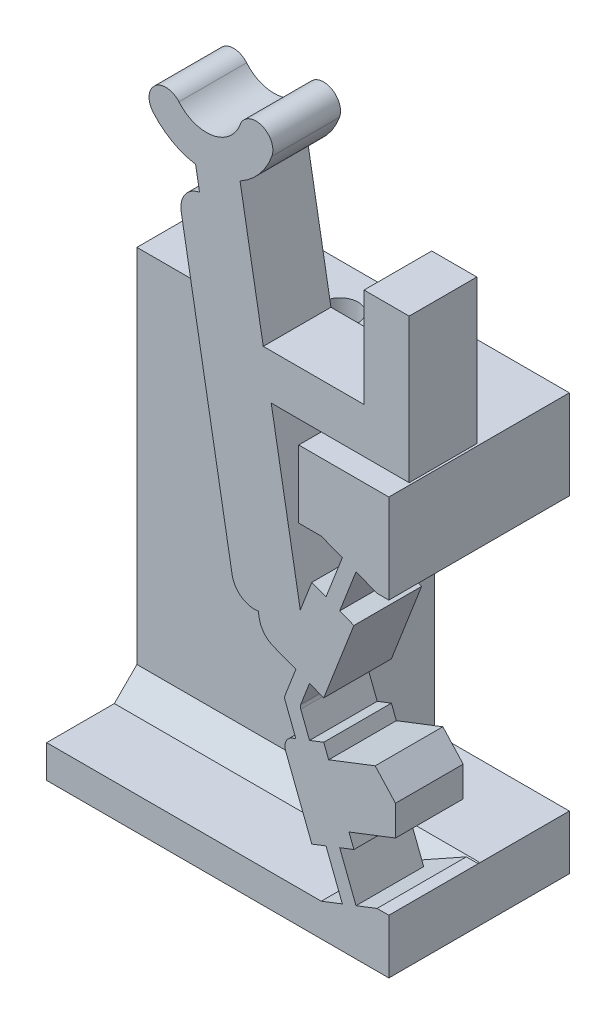
SolidWorks part; units mm, degrees
material "Nylon 6/12"
ref_plane "Front Plane" through (0, 0, 0) normal (0, 0, 1) x (1, 0, 0)
ref_plane "Top Plane" through (0, 0, 0) normal (0, 1, 0) x (1, 0, 0)
ref_plane "Right Plane" through (0, 0, 0) normal (1, 0, 0) x (0, 0, -1)
sketch "Sketch-SkeletonConfigUp" plane through (0, 0, 0) normal (0, 0, 1) x (1, 0, 0)
  line L0 (0, 0) -> (0, -50000) construction
  line L1 (-1.4217, 8.457) -> (-1.4217, 0) construction
  line L3 (0.7468, 14.0514) -> (-1.4217, 8.457) construction
  line L4 (-1.4217, 8.457) -> (0.7468, 2.8626) construction
  line L5 (0.7468, 14.0514) -> (2.1074, 19.3343) construction
  line L6 (-1.4217, 8.457) -> (-5.2203, 30) construction
  line L9 (0.7468, 14.0514) -> (0.7468, 2.8626) construction
  line L10 (0.7468, 2.8626) -> (0.7468, 0) construction
  line L11 (0, 0) -> (0.7468, 0) construction
  line L12 (0.7468, 0) -> (0, 0) construction
  dimension "D7" = 5.4552
  dimension "D10" = 6.745
  dimension "D3" = 2.1685
  dimension "D9" = 10
  dimension "D13" = 11.1888
  dimension "D14" = 30
  dimension "D5" = 10
  dimension "D2" = 21.8753
  dimension "D4" = 6
sketch "Sketch-SkeletonConfigDown" plane through (0, 0, 0) normal (0, 0, 1) x (1, 0, 0)
  line L0 (0, 0) -> (0, -50000) construction
  line L1 (0.7468, 14.0514) -> (0.7468, 2.8626) construction
  line L2 (5.9945, 14.5439) -> (0.7468, 14.0514) construction
  line L3 (0.7468, 14.0514) -> (2.9153, 8.457) construction
  line L4 (2.9153, 8.457) -> (0.7468, 2.8626) construction
  line L5 (0.7468, 14.0514) -> (-1.8086, 18.8711) construction
  line L6 (2.9153, 8.457) -> (-14.411, 21.8109) construction
  line L7 (0.7468, 2.8626) -> (5.9945, 14.5439) construction
  line L8 (-387.6937, -861.8102) -> (5.9945, 14.5439) construction
  line L10 (-1.4217, 8.457) -> (0.7468, 2.8626) construction
  line L11 (0.7468, 14.0514) -> (-1.4217, 8.457) construction
  line L12 (-1.4217, 8.457) -> (-5.2203, 30) construction
  line L13 (0.7468, 14.0514) -> (2.1074, 19.3343) construction
  dimension "D10" = 6.745
  dimension "D4" = 5.2707
  dimension "D5" = 119.553
  dimension "D2" = 52.378
  dimension "D3" = 31.19
ref_plane "Plane-Cam Base" through (3.8672, 0, 0) normal (1, 0, 0) x (0, 0, -1)
ref_plane "Plane-Down-to-Up Derailleur Clearance" through (1.3672, 0, 0) normal (1, 0, 0) x (0, 0, -1)
ref_plane "Plane-Cam Cavity Roof" through (-0.1328, 0, 0) normal (1, 0, 0) x (0, 0, -1)
sketch "Sketch-SwitchBossUp" plane through (0, 0, 0) normal (0, 0, 1) x (1, 0, 0)
  line L8 (-5.6979, 26.9497) -> (-5.5242, 25.9649)
  line L9 (-1.4217, 8.457) -> (-5.2203, 30) construction
  line L15 (-1.2549, 7.1274) -> (-0.6488, 7.3624) construction
  line L16 (-1.4217, 8.457) -> (0.7468, 2.8626) construction
  line L19 (0.0824, 13.2365) -> (0.6884, 13.0016) construction
  line L22 (0.8052, 15.1013) -> (1.4113, 14.8664) construction
  line L23 (-1.2549, 9.7866) -> (-1.8843, 10.0306)
  line L32 (1.0498, 2.9801) -> (0.4438, 2.7452) construction
  line L40 (-1.7703, 8.457) -> (-1.0732, 8.457) construction
  line L66 (-5.2203, 27.8193) -> (-5.2203, 50027.8193) construction
  line L74 (-4.078, 12.0039) -> (-6.3354, 24.8064)
  line L81 (2.3437, 2.4091) -> (2.8672, 2.4091)
  line L82 (-5.6111, 26.4573) -> (-3.6415, 26.8046) construction
  line L88 (-0.1116, 18.4627) -> (2.8672, 18.4627)
  line L92 (0.6492, 5.8814) -> (-1.2156, 5.1585) construction
  line L95 (-2.3469, 19.4627) -> (3.7672, 19.4627)
  line L96 (2.8672, 14.505) -> (2.8672, 18.4627)
  line L97 (3.7672, 19.4627) -> (3.7672, 25.8576)
  line L101 (-0.9519, 7.2449) -> (-1.4217, 8.457) construction
  line L103 (-5.2203, 30) -> (-3.0238, 29.2005) construction
  line L107 (-1.2549, 9.7866) -> (-0.6488, 9.5517) construction
  line L109 (-5.2203, 30) -> (-7.011, 28.4975) construction
  line L114 (-0.0195, 7.6063) -> (-0.6488, 7.3624)
  line L117 (2.8672, 0) -> (-0.1272, 0)
  line L121 (0.7468, 0) -> (0, 0) construction
  line L122 (0.8052, 1.8128) -> (-0.1272, 1.4513)
  line L123 (1.4113, 2.0477) -> (2.3437, 2.4091)
  line L125 (2.8672, 2.4091) -> (2.8672, 0)
  line L127 (-0.6488, 9.5517) -> (-0.0195, 9.3077)
  line L133 (0.4438, 14.1689) -> (1.0498, 13.934) construction
  line L134 (-0.0195, 9.3077) -> (1.3178, 12.7576)
  line L135 (0.6884, 13.0016) -> (1.3178, 12.7576)
  line L142 (-0.1272, 1.4513) -> (-0.1272, 0)
  line L151 (0.0824, 13.2365) -> (-0.547, 13.4805)
  line L152 (0.8052, 15.1013) -> (0.0824, 13.2365)
  line L153 (1.4113, 14.8664) -> (0.6884, 13.0016)
  line L169 (0.0824, 3.6776) -> (0.8052, 1.8128)
  line L170 (1.4113, 2.0477) -> (0.6884, 3.9125)
  line L177 (0.6884, 3.9125) -> (0.0824, 3.6776) construction
  line L184 (-0.547, 13.4805) -> (-1.0591, 12.1594)
  line L191 (-1.2549, 7.1274) -> (-1.8843, 6.8835)
  line L197 (3.7672, 25.8576) -> (1.7672, 25.8576)
  line L205 (1.7672, 25.8576) -> (1.7672, 21.4627)
  line L207 (12.0045, 16.6962) -> (12.0045, 16.6883) construction
  line L218 (0.6884, 3.9125) -> (1.3178, 4.1564)
  line L225 (-1.0591, 12.1594) -> (-2.3469, 19.4627)
  line L235 (-5.5242, 25.9649) -> (-2.7755, 10.376) construction
  line L236 (-1.8843, 6.8835) -> (-0.547, 3.4336)
  line L237 (-2.7755, 10.376) -> (-2.9195, 11.1927)
  line L241 (-1.4217, 8.457) -> (-0.9519, 9.6692) construction
  line L242 (1.7672, 21.4627) -> (-2.6996, 21.4627)
  line L243 (-0.6488, 7.3624) -> (-1.0381, 8.3667)
  line L244 (-1.0381, 8.5474) -> (-0.6488, 9.5517)
  line L245 (-1.2549, 7.1274) -> (-1.7353, 8.3667)
  line L246 (-1.7353, 8.5474) -> (-1.2549, 9.7866)
  line L247 (-0.0195, 7.6063) -> (0.1991, 7.0424)
  line L248 (0.8052, 1.8128) -> (1.4113, 2.0477) construction
  line L249 (0.0824, 3.6776) -> (-0.547, 3.4336)
  line L250 (-1.8843, 10.0306) -> (-0.547, 13.4805) construction
  line L251 (0.7468, 14.0514) -> (-1.4217, 8.457) construction
  line L252 (-1.2699, 11.6157) -> (0.5949, 10.8928) construction
  line L253 (-2.3469, 19.4627) -> (-2.6996, 21.4627) construction
  line L254 (-1.8843, 10.0306) -> (-2.7755, 10.376)
  line L255 (0.8052, 15.1013) -> (-0.1272, 15.4627)
  line L256 (1.4113, 14.8664) -> (2.3437, 14.505)
  line L257 (2.3437, 14.505) -> (2.8672, 14.505)
  line L258 (-2.6996, 21.4627) -> (-3.7283, 27.297)
  line L259 (3.8672, -55) -> (3.8672, 55) construction
  line L260 (0.1991, 7.0424) -> (2.2611, 7.8417)
  line L261 (3.1613, 6.8552) -> (3.1613, 5.5197)
  line L262 (3.1613, 5.5197) -> (1.0992, 4.7204)
  line L263 (0.6492, 5.8814) -> (3.1613, 6.8552) construction
  line L264 (1.0992, 4.7204) -> (0.6492, 5.8814) construction
  line L265 (1.0992, 4.7204) -> (1.3178, 4.1564)
  line L266 (0.6492, 5.8814) -> (0.1991, 7.0424) construction
  line L267 (0.1991, 7.0424) -> (0.6492, 5.8814) construction
  line L268 (0.6492, 5.8814) -> (1.0992, 4.7204) construction
  line L269 (0.1991, 7.0424) -> (0.6492, 5.8814) construction
  line L270 (0.6492, 5.8814) -> (1.0992, 4.7204) construction
  line L271 (3.1613, 6.8552) -> (2.2611, 7.8417)
  line L272 (1.8311, 5.6598) -> (3.8672, 4.8706) construction
  line L273 (2.9153, 8.457) -> (0.7468, 2.8626) construction
  line L274 (-0.2832, 5.52) -> (2.2611, 7.8417) construction
  line L275 (-0.2832, 5.52) -> (3.8672, 5.52) construction
  line L276 (-0.1272, 15.4627) -> (-1.1272, 15.4627)
  line L277 (-1.1272, 15.4627) -> (-1.1272, 18.4627)
  line L278 (-1.1272, 18.4627) -> (-0.1116, 18.4627)
  arc A0 (-3.7283, 27.297) -> (-2.319, 28.944) centre (-5.2203, 30) ccw
  arc A1 (-5.6979, 26.9497) -> (-7.5855, 28.0154) centre (-5.2203, 30) cw
  arc A2 (-7.5855, 28.0154) -> (-6.4364, 28.9796) centre (-7.011, 28.4975) cw
  arc A3 (-2.319, 28.944) -> (-3.7286, 29.457) centre (-3.0238, 29.2005) ccw
  arc A4 (-6.4364, 28.9796) -> (-3.7286, 29.457) centre (-5.2203, 30) ccw
  arc A19 (-6.3354, 24.8064) -> (-5.5242, 25.9649) centre (-5.3506, 24.98) cw
  circle A28 centre (-5.2203, 30) radius 2.3375 construction
  arc A30 (-4.078, 12.0039) -> (-2.9195, 11.1927) centre (-3.0932, 12.1775) ccw
  arc A31 (-1.0381, 8.3667) -> (-1.0381, 8.5474) centre (-0.805, 8.457) cw
  arc A32 (-1.7353, 8.3667) -> (-1.7353, 8.5474) centre (-1.5022, 8.457) cw
  point P5 (-4.6263, 26.6309)
  point P6 (-0.2832, 5.52)
  point P45 (-0.3375, 11.2542)
  point P66 (4.5811, 6.2164)
  point P165 (0.7468, 14.0514)
  dimension "D23" = 1.5875
  dimension "D24" = 0.75
  dimension "D21" = 0.25
  dimension "D8" = 0.65
  dimension "D27" = 0.65
  dimension "D26" = 2
  dimension "D3" = 1.3
  dimension "D5" = 1.3
  dimension "D16" = 2
  dimension "D28" = 2
  dimension "D29" = 2
  dimension "D30" = 1
  dimension "D31" = 15
  dimension "D4" = 1.4169
  dimension "D6" = 0.65
  dimension "D7" = 2
  dimension "D11" = 1
  dimension "D10" = 1
  dimension "D9" = 0
  dimension "D12" = 60
  dimension "D13" = 60
  dimension "D14" = 2
  dimension "D15" = 1
  dimension "D17" = 2
  dimension "D19" = 0.1
  dimension "D22" = 42.38
  dimension "D18" = 3
  dimension "D25" = 1
  dimension "D32" = 1
  dimension "D20" = 1
extrude "Boss-Switch Body" add sketch "Sketch-SwitchBossUp" along normal blind 3
sketch "Sketch1" plane through (0, 0, 0) normal (0, 0, -1) x (-1, 0, 0)
  line L0 (-2.8672, 2.4091) -> (0.1272, 2.4091)
  line L1 (-2.8672, 0) -> (0.1272, 0)
  line L2 (-2.8672, 0) -> (-2.8672, 2.4091)
  line L4 (0.1272, 0) -> (0.1272, 2.4091)
  line L5 (1.1272, 14.505) -> (-2.8672, 14.505)
  line L10 (-2.8672, 14.505) -> (-2.8672, 18.4627)
  line L12 (-2.8672, 18.4627) -> (1.1272, 18.4627)
  line L14 (1.1272, 18.4627) -> (1.1272, 14.505)
  line L20 (-2.3437, 2.4091) -> (-2.8672, 2.4091) construction
  line L22 (-2.8672, 2.4091) -> (-2.3437, 2.4091) construction
  line L31 (0.1272, 0) -> (-2.8672, 0) construction
  line L32 (0.1272, 1.4513) -> (0.1272, 0) construction
extrude "Boss-Flange Width" add sketch "Sketch1" along normal blind 5
ref_plane "Plane-Sta2Sit Groove" through (-5.2203, 0, 0) normal (1, 0, 0) x (0, 0, -1)
ref_plane "Plane-Cam Outer Surface" through (-17.3003, 0, 0) normal (1, 0, 0) x (0, 0, -1)
ref_plane "Plane-FlangeTop" through (-12.3003, 0, 0) normal (1, 0, 0) x (0, 0, -1)
sketch "Sketch2" plane through (-12.3003, 0, 0) normal (1, 0, 0) x (0, 0, -1)
  line L0 (5, 18.4627) -> (-3, 18.4627) construction
  line L1 (5, 14.505) -> (1, 14.505)
  line L2 (5, 14.505) -> (5, 18.4627)
  line L3 (5, 18.4627) -> (1, 18.4627)
  line L4 (1, 14.505) -> (1, 18.4627)
  line L5 (5, 14.505) -> (-3, 14.505) construction
  line L11 (5, 1.4513) -> (-3, 1.4513)
  line L12 (5, 1.4513) -> (5, 0)
  line L13 (5, 0) -> (-3, 0)
  line L14 (-3, 1.4513) -> (-3, 0)
  line L15 (0, 8.457) -> (0, 30) construction
  line L16 (-3, 1.4513) -> (-3, 0) construction
  line L17 (5, 2.4091) -> (5, 0) construction
  line L19 (-3, 1.4513) -> (0, 1.4513) construction
  dimension "D1" = 1
extrude "Boss-Flange Height" add sketch "Sketch2" along normal up to surface (12.1731 mm away) up to face at (-0.1272, 1.2868, -0.6667)
sketch "Sketch17" plane through (0, 1.4513, 0) normal (0, -1, 0) x (1, 0, 0)
  line L0 (2.8672, -5) -> (-12.3003, -5)
  line L1 (2.8672, -5) -> (-12.3003, -5) construction
  line L2 (-12.3003, -5) -> (-12.3003, -1)
  line L3 (-12.3003, -1) -> (2.8672, -1)
  line L4 (2.8672, -1) -> (2.8672, -5)
  line L5 (-12.3003, -1) -> (-12.3003, -5) construction
  line L7 (-1.1272, -1) -> (-12.3003, -1) construction
extrude "Boss-Flange Support" add sketch "Sketch17" against normal up to surface (13.0536 mm away) up to face at (-1.4588, 14.505, -0.6)
sketch "Sketch27" plane through (0, 0, 0) normal (0, 0, 1) x (1, 0, 0)
  line L1 (-0.1272, 15.4627) -> (2.3437, 14.505)
  line L2 (2.3437, 14.505) -> (-1.1272, 14.505)
  line L3 (-1.1272, 14.505) -> (-1.1272, 15.4627)
  line L4 (-1.1272, 15.4627) -> (-0.1272, 15.4627)
  line L6 (-1.1272, 14.505) -> (2.8672, 14.505) construction
  line L7 (2.3437, 14.505) -> (1.2712, 14.505) construction
  line L8 (2.3437, 2.4091) -> (-0.1272, 2.4091)
  line L9 (-0.1272, 2.4091) -> (-0.1272, 1.4513)
  line L10 (-0.1272, 1.4513) -> (2.3437, 2.4091)
extrude "Cut-Wall Gap" cut sketch "Sketch27" against normal up to surface (1 mm away) up to face at (-2.6719, 9.207, -1)
ref_plane "Plane-Tap Depth" through (0, 13.4627, 0) normal (0, 1, 0) x (1, 0, 0)
sketch "Sketch-HolePositions" plane through (0, 0, 0) normal (0, -1, 0) x (1, 0, 0)
  line L0 (-12.3003, -3) -> (2.8672, -3) construction
  line L1 (2.8672, -5) -> (-12.3003, -5) construction
  line L2 (2.8672, -5) -> (2.8672, 3) construction
  line L4 (-12.3003, -22.2167) -> (-12.3003, 22.2167) construction
  point P6 (-9.3003, -3)
  point P7 (-5.3003, -3)
  dimension "D1" = 3
  dimension "D2" = 4
  dimension "D3" = 2
sketch "Sketch6" plane through (0, 0, 0) normal (0, -1, 0) x (-1, 0, 0)
  point P0 (9.3003, 3)
  point P3 (5.3003, 3)
hole_wizard "Tap Drill for M2x0.4 Tap1" positions "Sketch6" profile "Sketch5" hole size "M2x0.4" standard "ANSI Metric" end condition through all
sketch "Sketch5" plane through (-9.3003, 0, -3) normal (1, 0, 0) x (0, 0, -1)
  line L0 (0, 0) -> (0, 29.9505)
  line L1 (0, 29.9505) -> (0.8, 29.9505)
  line L2 (0.8, 29.9505) -> (0.8, 0)
  line L5 (0.8, 0) -> (0, 0)
  line L11 (0, -6.35) -> (0, 107.95) construction
  dimension "Thru Hole Dia." = 1.6
  dimension "Thru Hole Depth" = 29.9505
sketch "Sketch9" plane through (0, 0, 0) normal (0, -1, 0) x (1, 0, 0)
  point P0 (-9.3003, -3)
  point P3 (-5.3003, -3)
hole_wizard "M2 Clearance Hole2" positions "Sketch9" profile "Sketch8" hole size "M2" standard "ANSI Metric"
sketch "Sketch8" plane through (-9.3003, 0, -3) normal (1, 0, 0) x (0, 0, -1)
  line L0 (0, 0) -> (0, 14.1838)
  line L1 (0, 14.1838) -> (1.2, 13.4627)
  line L2 (1.2, 13.4627) -> (1.2, 0)
  line L5 (1.2, 0) -> (0, 0)
  line L10 (0, 14.1838) -> (-1.2, 13.4627) construction
  line L11 (0, -6.35) -> (0, 107.95) construction
  dimension "Hole Dia." = 2.4
  dimension "Hole Depth" = 13.4627
  dimension "Drill Angle" = 118
sketch "Sketch-Measurements for Derailleur Ramps" [suppressed] plane through (0, 0, 0) normal (0, 0, 1) x (1, 0, 0)
  line L0 (2.8784, 16.9852) -> (4.2265, 19.8331)
  line L1 (3.5524, 18.4092) -> (3.0492, 18.6474)
  line L2 (1.9779, 11.0613) -> (4.4465, 28.5428) construction
  line L3 (3.0492, 18.6474) -> (-4.0642, 13.8428)
  line L4 (7.1843, 11.0614) -> (-9.9544, 15.2993) construction
  line L5 (3.0492, 18.6474) -> (2.1536, 12.3053)
  line L6 (2.1536, 12.3053) -> (-4.0642, 13.8428)
  line L7 (-0.5075, 16.2451) -> (-0.5075, 18.6474)
  line L8 (-0.5075, 18.6474) -> (3.0492, 18.6474)
  line L9 (7.1843, 11.0614) -> (1.9779, 11.0613)
  line L10 (5.8827, 8.6389) -> (3.2795, 8.6389)
  line L12 (7.1843, 11.0614) -> (4.5811, 6.2164) construction
  line L13 (4.5811, 8.6389) -> (4.5811, 8.7912)
  line L14 (4.5811, 6.2164) -> (5.8827, 8.6389)
  line L15 (1.9779, 11.0613) -> (4.5811, 6.2164) construction
  line L16 (3.2795, 8.6389) -> (4.5811, 6.2164)
  line L17 (5.8827, 8.6389) -> (5.8827, 8.7912)
  dimension "D1" = 3.5567
  dimension "D2" = 1.3016
sketch "Sketch12" [suppressed] plane through (0, 23.1883, 0) normal (0, 1, 0) x (1, 0, 0)
  line L0 (10.0045, 0) -> (12.0045, -3)
  line L1 (12.0045, -3) -> (12.0045, 0)
  line L2 (12.0045, 0) -> (10.0045, 0)
extrude "Cut-Up-to-Down Cantilever Slope" [suppressed] cut sketch "Sketch12" against normal up to next
ref_plane "Plane1" [suppressed] through (0, 6.9404, 0) normal (0, 1, 0) x (1, 0, 0)
sketch "Sketch-Derailleur Location" [suppressed] plane through (0, 6.9404, 0) normal (0, 1, 0) x (1, 0, 0)
  line L0 (12.9465, 0) -> (12.9465, -3)
  line L1 (4.2399, -3) -> (3.2603, -3) construction
  line L2 (-119237.4187, 0) -> (9.8143, 0) construction
  point P0 (12.9465, 0)
  point P8 (12.9465, -1.5)
ref_plane "Plane-Cantilever Cut" [suppressed] through (7.0848, 8.5204, -1.9058) normal (-0.6301, -0.7578, 0.1695) x (-0.7765, 0.6151, -0.1368)
sketch "Sketch14" [suppressed] plane through (7.0848, 8.5204, -1.9058) normal (-0.6301, -0.7578, 0.1695) x (-0.7765, 0.6151, -0.1368)
  line L0 (2.3023, -1.6911) -> (-0.3551, -1.6911)
  line L2 (2.3023, -4.3362) -> (2.3023, -1.6911)
  line L3 (-0.3551, -1.6911) -> (-0.3551, -4.4608)
  line L5 (-0.3551, -4.4608) -> (1.0087, -5.0843)
  line L6 (1.0087, -5.0843) -> (2.3023, -4.3362)
extrude "Cut-Down-to-Up Cantilever Slope" [suppressed] cut sketch "Sketch14" against normal up to next
ref_plane "Plane-Symmetry Plane" through (0, 0, 1.5) normal (0, 0, 1) x (1, 0, 0)
sketch "Sketch-Cable Center Point" plane through (0, 0, 1.5) normal (0, 0, 1) x (1, 0, 0)
  line L0 (-5.2203, 30) -> (-5.0825, 29.2183)
  line L1 (-1.4217, 8.457) -> (-5.2203, 30) construction
  point P0 (-5.2203, 30)
  dimension "D1" = 0.7937
sketch "Sketch28" plane through (0, 0, -1) normal (0, 0, 1) x (1, 0, 0)
  line L0 (2.8672, 14.505) -> (2.8672, 2.4091)
  line L1 (2.3437, 2.4091) -> (2.8672, 2.4091) construction
  line L2 (2.8672, 14.505) -> (-3.1003, 14.505)
  line L3 (-3.1003, 14.505) -> (-3.1003, 2.4091)
  line L4 (-3.1003, 2.4091) -> (2.8672, 2.4091)
  line L6 (-6.5003, 13.4627) -> (-4.1003, 13.4627) construction
  line L7 (-6.5003, 13.4627) -> (-4.1003, 13.4627) construction
  dimension "D1" = 1
chamfer "Chamfer-Flange Support" [suppressed] distance 1.5 angle 45
chamfer "Chamfer-Flange Support 3" distance 1 angle 45 1 edges at (-6.2138, 1.4513, -1)
fillet "Fillet1" radius 1 1 edges at (-2.7755, 10.376, 1.5)
fillet "Fillet2" radius 0.5 1 edges at (-1.8843, 6.8835, 1.5)
extrude "Cut-Print Support Clearance" cut sketch "Sketch28" against normal through all
equation "\"axle-diameter\"=2"
equation "\"switch-thickness\"=12"
equation "\"base-width\"=4.0"
equation "\"axle-bushing-radius\"=3"
equation "\"clearance\"= 0.25"
equation "\"arm-width\"=1.5"
equation "\"min-diameter\"=70"
equation "\"alpha\"=143.6120"
equation "\"gamma\"=119.5526"
equation "\"delta\"=145.9637"
equation "\"epsilon\"=6.7452"
equation "\"l_AB\"=8.8212"
equation "\"l_AC\"=4.4914"
equation "\"l_BD\"=5.2707"
equation "\"l_CD\"=3.8848"
equation "\"l_CE\"=10.9181"
equation "\"l_DF\"=5.4552"
equation "\"l_OA\"=7.7221"
equation "\"D7@Sketch-SkeletonConfigUp\" = \"l_DF\""
equation "\"D_groove\"=3.175"
equation "\"D5@Sketch-SkeletonConfigDown\" = \"gamma\""
equation "\"D4@Sketch-SkeletonConfigDown\" = \"l_BD\""
equation "\"hinge_length\"=1.5"
equation "\"hinge_depth\"=0.25"
equation "\"D10@Sketch-SkeletonConfigUp\"=\"epsilon\""
equation "\"D10@Sketch-SkeletonConfigDown\"=\"epsilon\""
equation "\"EE_dx\"=8.9056"
equation "\"EE_dy\"=8.1898"
equation "\"r_groove\"=\"D_groove\"/2"
equation "\"t_wall\"=25.4/16"
equation "\"width_lower\"=\"D_groove\"+\"t_wall\""
equation "\"cable_to_bottom\"=30.6257"
equation "\"switch_EE-up_base_dy\"=24"
equation "\"switch_EE-down_base_dy\"=16"
equation "\"D_axle\"=25.4/8"
equation "\"D_up_to_down\"=16"
equation "\"D_down_to_up\"=25"
equation "\"t_cam_base\"=7.5"
equation "\"D23@Sketch-SwitchBossUp\"=\"D_groove\"/2"
equation "\"D1@Sketch-Cable Center Point\"=\"D_groove\"/4"
